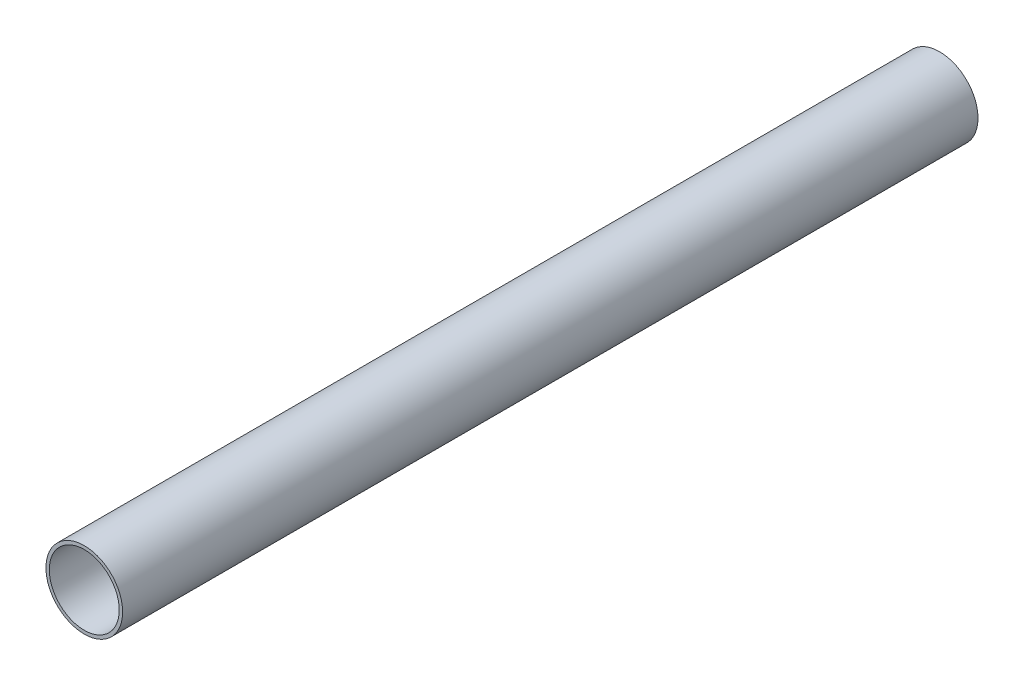
SolidWorks part; units mm, degrees
ref_plane "Front Plane" through (0, 0, 0) normal (0, 0, 1) x (1, 0, 0)
ref_plane "Top Plane" through (0, 0, 0) normal (0, 1, 0) x (1, 0, 0)
ref_plane "Right Plane" through (0, 0, 0) normal (1, 0, 0) x (0, 0, -1)
sketch "Sketch1" plane through (0, 0, 0) normal (0, 0, 1) x (1, 0, 0)
  circle A0 centre (0, 0) radius 15.9385
  circle A1 centre (0, 0) radius 14.5415
  dimension "D1" = 29.083
  dimension "D2" = 31.877
extrude "Boss-Extrude1" add sketch "Sketch1" along normal blind 355.6
